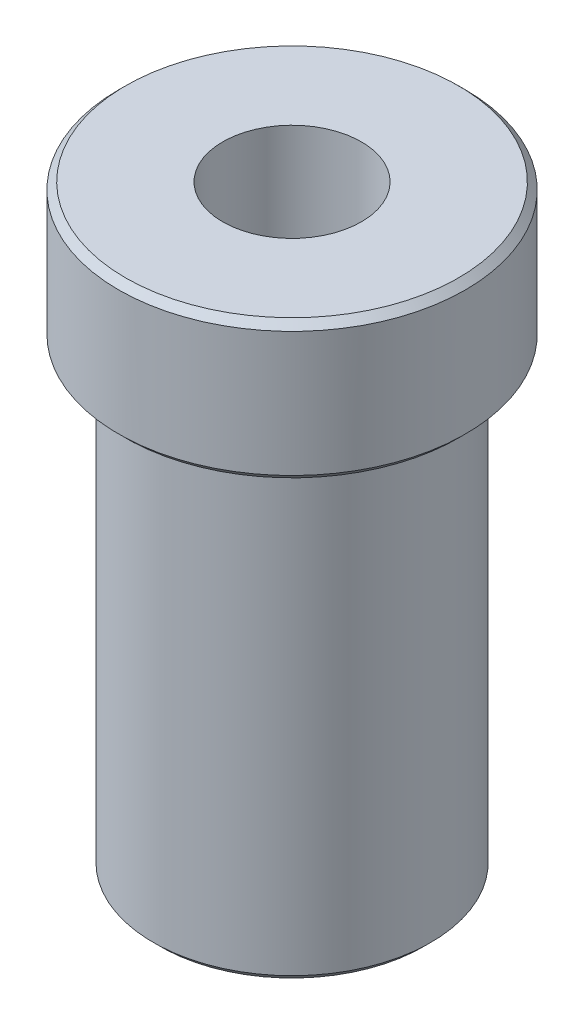
SolidWorks part; units mm, degrees
ref_plane "Front Plane" through (0, 0, 0) normal (0, 0, 1) x (1, 0, 0)
ref_plane "Top Plane" through (0, 0, 0) normal (0, 1, 0) x (1, 0, 0)
ref_plane "Right Plane" through (0, 0, 0) normal (1, 0, 0) x (0, 0, -1)
sketch "Sketch1" plane through (0, 0, 0) normal (0, 0, 1) x (1, 0, 0)
  line L0 (-2.8465, 10) -> (9.6535, 10)
  line L1 (9.6535, 10) -> (9.6535, 0)
  line L2 (9.6535, 0) -> (7.1535, 0)
  line L3 (7.1535, 0) -> (7.1535, -33)
  line L4 (7.1535, -33) -> (-2.8465, -33)
  line L5 (-2.8465, -33) -> (-2.8465, 10)
  dimension "D1" = 12.5
  dimension "D2" = 10
  dimension "D3" = 33
  dimension "D4" = 10
revolve "Revolve1" add sketch "Sketch1" angle 360 about L5
sketch "Sketch2" plane through (0, 10, 0) normal (0, 1, 0) x (1, 0, 0)
  circle A0 centre (-2.8465, 0) radius 5
  dimension "D1" = 10
extrude "Cut-Extrude1" cut sketch "Sketch2" against normal through all
chamfer "Chamfer1" distance 0.5 angle 45 3 edges at (-2.8465, -33, -10) (-2.8465, 0, -12.5) (-2.8465, 10, -12.5)
